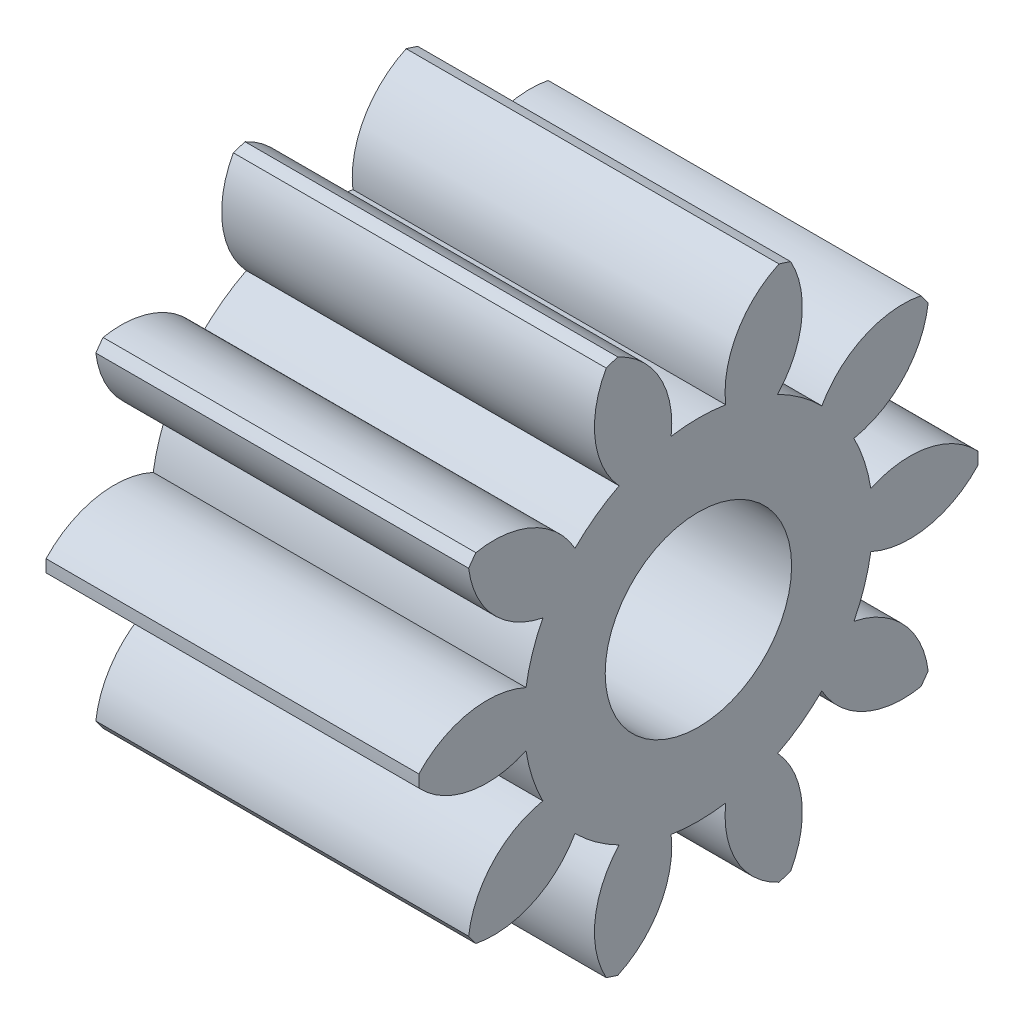
SolidWorks part; units mm, degrees
ref_plane "Plan de face" through (0, 0, 0) normal (0, 0, 1) x (1, 0, 0)
ref_plane "Plan de dessus" through (0, 0, 0) normal (0, 1, 0) x (1, 0, 0)
ref_plane "Plan de droite" through (0, 0, 0) normal (1, 0, 0) x (0, 0, -1)
ref_plane "Plan1" through (0, 0, 0) normal (-1, 0, 0) x (0, -1, 0)
sketch "Esquisse1" plane through (0, 0, 0) normal (-1, 0, 0) x (0, -1, 0)
  arc A0 (-0.9081, -1.1939) -> (-0.8548, -1.2326) centre (0, 0) ccw
  arc A1 (-0.8548, -1.2326) -> (-0.425, -0.8345) centre (-0.9152, -0.7362) ccw
  arc A2 (-0.425, -0.8345) -> (-0.1467, -0.9249) centre (0, 0) ccw
  arc A3 (-0.1467, -0.9249) -> (-0.0329, -1.4996) centre (0.3077, -1.1336) ccw
  arc A4 (-0.0329, -1.4996) -> (0.0329, -1.4996) centre (0, 0) ccw
  arc A5 (0.0329, -1.4996) -> (0.1467, -0.9249) centre (-0.3077, -1.1336) ccw
  arc A6 (0.1467, -0.9249) -> (0.425, -0.8345) centre (0, 0) ccw
  arc A7 (0.425, -0.8345) -> (0.8548, -1.2326) centre (0.9152, -0.7362) ccw
  arc A8 (0.8548, -1.2326) -> (0.9081, -1.1939) centre (0, 0) ccw
  arc A9 (0.9081, -1.1939) -> (0.6623, -0.6621) centre (0.4174, -1.098) ccw
  arc A10 (0.6623, -0.6621) -> (0.8343, -0.4253) centre (0, 0) ccw
  arc A11 (0.8343, -0.4253) -> (1.4161, -0.4947) centre (1.1732, -0.0577) ccw
  arc A12 (1.4161, -0.4947) -> (1.4364, -0.4321) centre (0, 0) ccw
  arc A13 (1.4364, -0.4321) -> (0.925, -0.1463) centre (0.983, -0.6429) ccw
  arc A14 (0.925, -0.1463) -> (0.925, 0.1463) centre (0, 0) ccw
  arc A15 (0.925, 0.1463) -> (1.4364, 0.4321) centre (0.983, 0.6429) ccw
  arc A16 (1.4364, 0.4321) -> (1.4161, 0.4947) centre (0, 0) ccw
  arc A17 (1.4161, 0.4947) -> (0.8343, 0.4253) centre (1.1732, 0.0577) ccw
  arc A18 (0.8343, 0.4253) -> (0.6623, 0.6621) centre (0, 0) ccw
  arc A19 (0.6623, 0.6621) -> (0.9081, 1.1939) centre (0.4174, 1.098) ccw
  arc A20 (0.9081, 1.1939) -> (0.8548, 1.2326) centre (0, 0) ccw
  arc A21 (0.8548, 1.2326) -> (0.425, 0.8345) centre (0.9152, 0.7362) ccw
  arc A22 (0.425, 0.8345) -> (0.1467, 0.9249) centre (0, 0) ccw
  arc A23 (0.1467, 0.9249) -> (0.0329, 1.4996) centre (-0.3077, 1.1336) ccw
  arc A24 (0.0329, 1.4996) -> (-0.0329, 1.4996) centre (0, 0) ccw
  arc A25 (-0.0329, 1.4996) -> (-0.1467, 0.9249) centre (0.3077, 1.1336) ccw
  arc A26 (-0.1467, 0.9249) -> (-0.425, 0.8345) centre (0, 0) ccw
  arc A27 (-0.425, 0.8345) -> (-0.8548, 1.2326) centre (-0.9152, 0.7362) ccw
  arc A28 (-0.8548, 1.2326) -> (-0.9081, 1.1939) centre (0, 0) ccw
  arc A29 (-0.9081, 1.1939) -> (-0.6623, 0.6621) centre (-0.4174, 1.098) ccw
  arc A30 (-0.6623, 0.6621) -> (-0.8343, 0.4253) centre (0, 0) ccw
  arc A31 (-0.8343, 0.4253) -> (-1.4161, 0.4947) centre (-1.1732, 0.0577) ccw
  arc A32 (-1.4161, 0.4947) -> (-1.4364, 0.4321) centre (0, 0) ccw
  arc A33 (-1.4364, 0.4321) -> (-0.925, 0.1463) centre (-0.983, 0.6429) ccw
  arc A34 (-0.925, 0.1463) -> (-0.925, -0.1463) centre (0, 0) ccw
  arc A35 (-0.925, -0.1463) -> (-1.4364, -0.4321) centre (-0.983, -0.6429) ccw
  arc A36 (-1.4364, -0.4321) -> (-1.4161, -0.4947) centre (0, 0) ccw
  arc A37 (-1.4161, -0.4947) -> (-0.8343, -0.4253) centre (-1.1732, -0.0577) ccw
  arc A38 (-0.8343, -0.4253) -> (-0.6623, -0.6621) centre (0, 0) ccw
  arc A39 (-0.6623, -0.6621) -> (-0.9081, -1.1939) centre (-0.4174, -1.098) ccw
  circle A40 centre (0, 0) radius 0.5
extrude "Boss.-Extru.1" add sketch "Esquisse1" against normal blind 2
